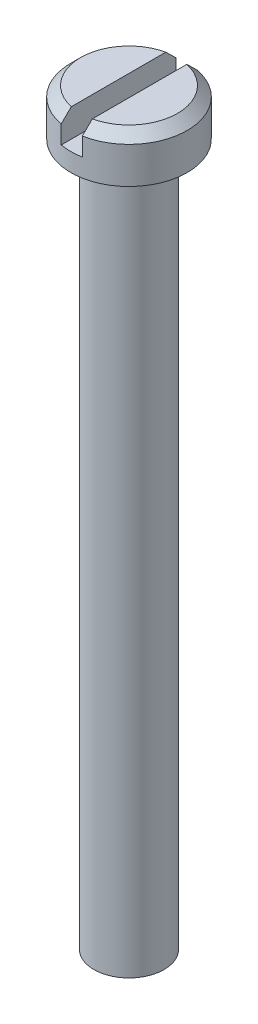
SolidWorks part; units mm, degrees
ref_plane "Front Plane" through (0, 0, 0) normal (0, 0, 1) x (1, 0, 0)
ref_plane "Top Plane" through (0, 0, 0) normal (0, 1, 0) x (1, 0, 0)
ref_plane "Right Plane" through (0, 0, 0) normal (1, 0, 0) x (0, 0, -1)
sketch "Sketch1" plane through (0, 0, 0) normal (0, 0, 1) x (1, 0, 0)
  line L0 (0, 0) -> (0, 13.0102) construction
  line L2 (0, 53.3) -> (4.15, 53.3)
  line L3 (0, 53.3) -> (0, 50)
  line L4 (2.5, 50) -> (4.15, 50)
  line L5 (4.15, 53.3) -> (4.15, 50)
  line L7 (0, 50) -> (0, 0)
  line L8 (0, 0) -> (2.5, 0)
  line L9 (2.5, 50) -> (2.5, 0)
  dimension "D1" = 8.3
  dimension "D2" = 5
  dimension "D3" = 3.3
  dimension "D4" = 50
revolve "Revolve1" add sketch "Sketch1" angle 360 about L0
chamfer "Chamfer1" distance 0.7 angle 45 1 edges at (0, 53.3, -4.15)
sketch "Sketch2" plane through (0, 0, 0) normal (0, 0, 1) x (1, 0, 0)
  line L0 (3.45, 53.3) -> (-3.45, 53.3) construction
  line L1 (0.7535, 58.0872) -> (-0.7465, 58.0872)
  line L2 (0.7535, 58.0872) -> (0.7535, 51.3)
  line L3 (0.7535, 51.3) -> (-0.7465, 51.3)
  line L4 (-0.7465, 58.0872) -> (-0.7465, 51.3)
  line L5 (0.7535, 58.0872) -> (-0.7465, 51.3) construction
  line L6 (0.7535, 51.3) -> (-0.7465, 58.0872) construction
  point P0 (0.0035, 54.6936)
  dimension "D1" = 1.5
  dimension "D2" = 2
extrude "Cut-Extrude1" cut sketch "Sketch2" against normal blind 19 and the other way blind 50
